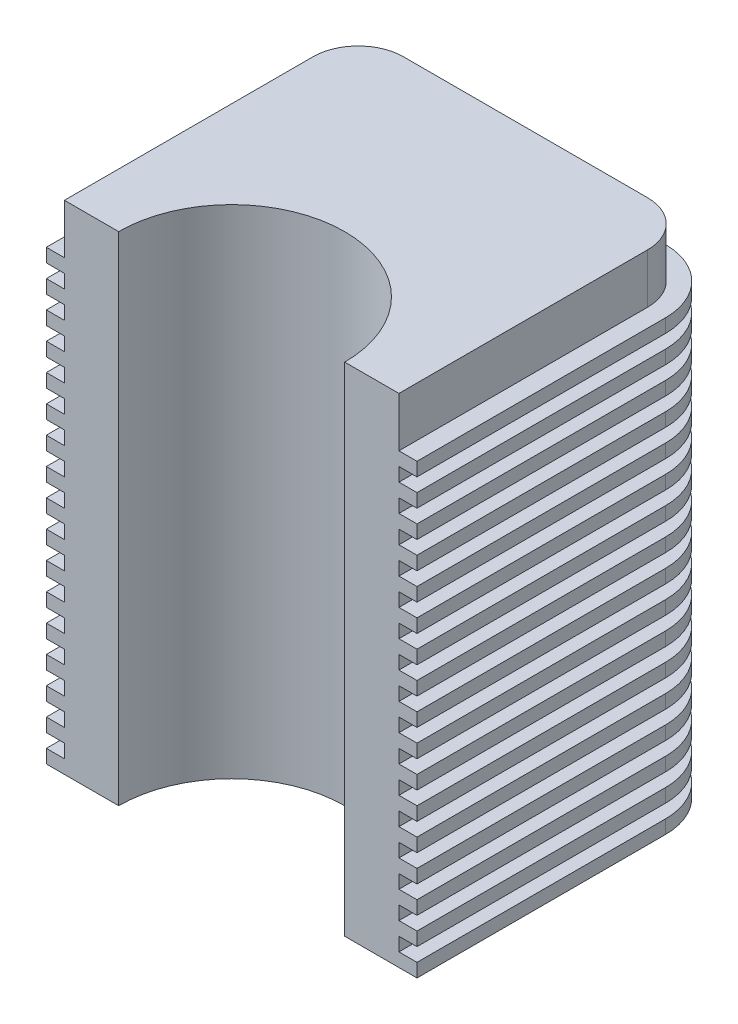
SolidWorks part; units mm, degrees
ref_plane "Front Plane" through (0, 0, 0) normal (0, 0, 1) x (1, 0, 0)
ref_plane "Top Plane" through (0, 0, 0) normal (0, 1, 0) x (1, 0, 0)
ref_plane "Right Plane" through (0, 0, 0) normal (1, 0, 0) x (0, 0, -1)
sketch "Sketch1" plane through (0, 0, 0) normal (0, 1, 0) x (1, 0, 0)
  line L0 (635, 0) -> (939.8, 0)
  line L1 (939.8, 0) -> (939.8, 1397)
  line L2 (685.8, 1651) -> (-685.8, 1651)
  line L3 (0, 0) -> (0, 1031.1985) construction
  line L4 (-939.8, 0) -> (-939.8, 1397)
  line L5 (-635, 0) -> (-939.8, 0)
  arc A0 (635, 0) -> (-635, 0) centre (0, 0) ccw
  arc A1 (939.8, 1397) -> (685.8, 1651) centre (685.8, 1397) ccw
  arc A2 (-939.8, 1397) -> (-685.8, 1651) centre (-685.8, 1397) cw
  point P9 (0, 1651)
  point P12 (939.8, 1651)
  point P15 (-939.8, 1651)
  point P16 (0, 0)
  dimension "D1" = 1270
  dimension "D4" = 254
  dimension "D2" = 304.8
  dimension "D3" = 1651
extrude "Boss-Extrude1" add sketch "Sketch1" along normal blind 2794
sketch "Sketch2" plane through (0, 0, 0) normal (0, -1, 0) x (1, 0, 0)
  line L0 (1041.4, -1397) -> (1041.4, 0)
  line L3 (-1041.4, 0) -> (-1041.4, -1397)
  line L4 (-685.8, -1752.6) -> (685.8, -1752.6)
  line L5 (939.8, -1397) -> (939.8, 0)
  line L6 (939.8, 0) -> (635, 0)
  line L7 (-635, 0) -> (-939.8, 0)
  line L8 (-939.8, 0) -> (-939.8, -1397)
  line L9 (-685.8, -1651) -> (685.8, -1651)
  line L10 (939.8, -1397) -> (939.8, 0)
  line L11 (939.8, 0) -> (635, 0)
  line L12 (-635, 0) -> (-939.8, 0)
  line L13 (-939.8, 0) -> (-939.8, -1397)
  line L14 (-685.8, -1651) -> (685.8, -1651)
  line L15 (-939.8, 0) -> (-1041.4, 0)
  line L16 (939.8, 0) -> (1041.4, 0)
  line L17 (1041.4, -1397) -> (1041.4, 101.6) construction
  line L18 (-1041.4, 101.6) -> (-1041.4, -1397) construction
  line L20 (-523.6344, 101.6) -> (-1041.4, 101.6) construction
  line L21 (1041.4, 101.6) -> (523.6344, 101.6) construction
  arc A0 (685.8, -1752.6) -> (1041.4, -1397) centre (685.8, -1397) ccw
  arc A2 (-1041.4, -1397) -> (-685.8, -1752.6) centre (-685.8, -1397) ccw
  arc A3 (685.8, -1651) -> (939.8, -1397) centre (685.8, -1397) ccw
  arc A4 (-635, 0) -> (635, 0) centre (0, 0) ccw
  arc A5 (-939.8, -1397) -> (-685.8, -1651) centre (-685.8, -1397) ccw
  arc A6 (685.8, -1651) -> (939.8, -1397) centre (685.8, -1397) ccw
  arc A7 (-635, 0) -> (635, 0) centre (0, 0) ccw
  arc A8 (-939.8, -1397) -> (-685.8, -1651) centre (-685.8, -1397) ccw
  arc A12 (-523.6344, 101.6) -> (523.6344, 101.6) centre (0, 0) ccw construction
  arc M17 (685.8, -1651) -> (939.8, -1397) centre (685.8, -1397) ccw
  line M18 (939.8, -1397) -> (939.8, 0)
  line M22 (-939.8, 0) -> (-939.8, -1397)
  arc M23 (-939.8, -1397) -> (-685.8, -1651) centre (-685.8, -1397) ccw
  line M24 (-685.8, -1651) -> (685.8, -1651)
  dimension "D1" = 0
  dimension "D2" = 101.6
extrude "Boss-Extrude2" add sketch "Sketch2" against normal blind 76.2 contours L3 A2 L4 A0 L0 L16 L15 M18 M17 M24 M23 M22
pattern_linear "LPattern1" count 17 spacing 152.4 along (0, 1, 0) of "Boss-Extrude2"
